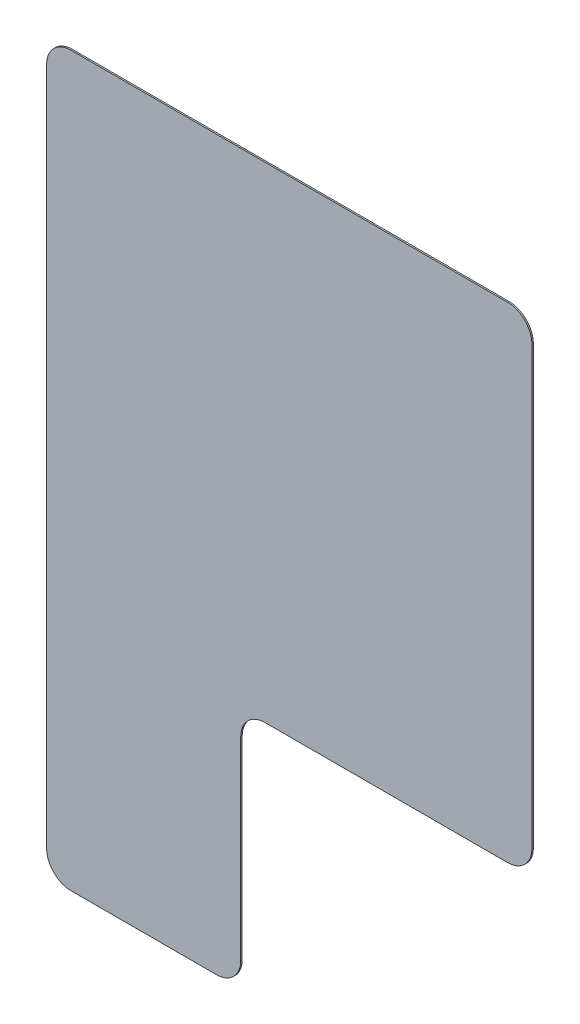
SolidWorks part; units mm, degrees
material "Copper"
ref_plane "Front Plane" through (0, 0, 0) normal (0, 0, 1) x (1, 0, 0)
ref_plane "Top Plane" through (0, 0, 0) normal (0, 1, 0) x (1, 0, 0)
ref_plane "Right Plane" through (0, 0, 0) normal (1, 0, 0) x (0, 0, -1)
sketch "Sketch1" plane through (0, 0, 0) normal (0, 0, 1) x (1, 0, 0)
  line L1 (-2.5, -2.5) -> (2.5, -2.5)
  line L2 (-2.5, -2.5) -> (-2.5, 2.5)
  line L3 (-2.5, 2.5) -> (2.5, 2.5)
  line L4 (2.5, -2.5) -> (2.5, 2.5)
  line L5 (-2.5, -2.5) -> (2.5, 2.5) construction
  line L6 (-2.5, 2.5) -> (2.5, -2.5) construction
  line L7 (-2.5, -2.5) -> (-0.5, -2.5)
  line L8 (-2.5, -2.5) -> (-2.5, -5)
  line L9 (-2.5, -5) -> (-0.5, -5)
  line L10 (-0.5, -2.5) -> (-0.5, -5)
  point P0 (0, 0)
  dimension "D1" = 5
  dimension "D2" = 2.5
  dimension "D3" = 2
extrude "Boss-Extrude1" add sketch "Sketch1" along normal blind 0.015 contours L10 L1 L8 L9 | L1 L4 L3 L2
fillet "Fillet1" radius 0.25 6 edges at (2.5, 2.5, 0.0075) (-2.5, 2.5, 0.0075) (-2.5, -5, 0.0075) (-0.5, -5, 0.0075) (-0.5, -2.5, 0.0075) (2.5, -2.5, 0.0075)
